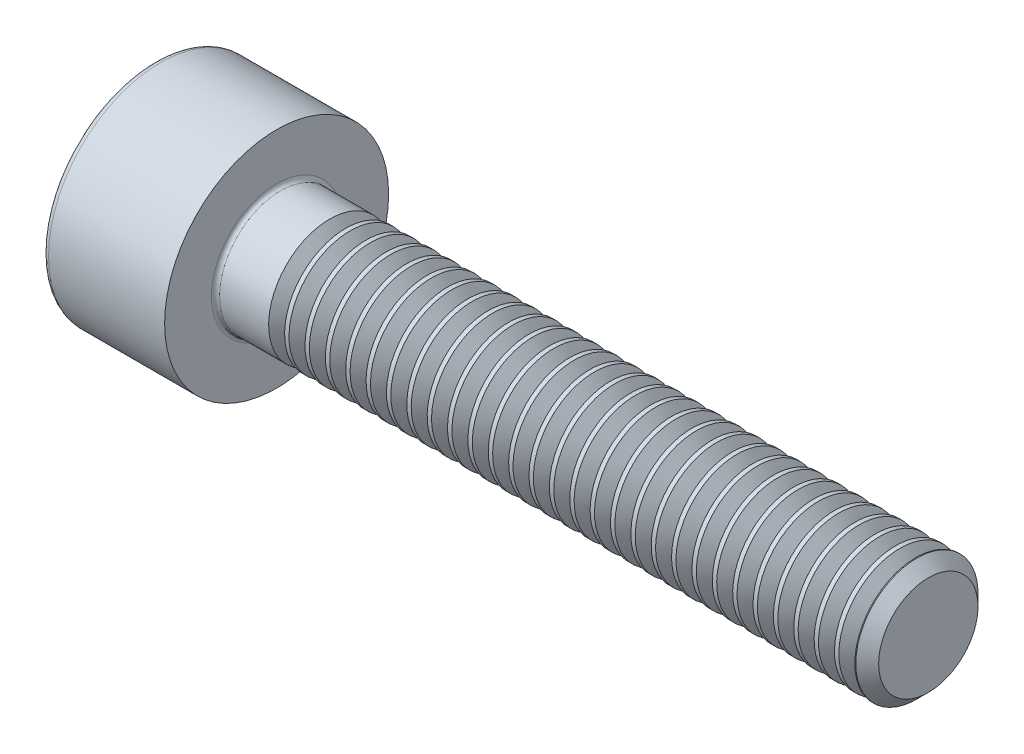
SolidWorks part; units mm, degrees
revolve "Base-Revolve" add sketch "BodySke"
sketch "BodySke" plane through (0, 0, 0) normal (0, 0, 1) x (1, 0, 0)
  line L0 (0, 0) -> (0, 2.75)
  line L1 (0, 2.75) -> (3, 2.75)
  line L2 (3, 2.75) -> (3, 1.5)
  line L3 (3, 1.5) -> (18.7195, 1.5)
  line L4 (19, 1.2195) -> (19, 0)
  line L5 (19, 0) -> (0, 0)
  line L6 (-31.75, 0) -> (127, 0) construction
  line L8 (19, 1.2195) -> (18.7195, 1.5)
  line L10 (19, -1.2195) -> (18.7195, -1.5) construction
  line L11 (3.5, 9.525) -> (3.5, 3.175) construction
  line L12 (3, 9.525) -> (3, 3.175) construction
  line L13 (-41, 9.525) -> (-41, 3.175) construction
  dimension "Head_ht" = 3
  dimension "Length" = 16
  dimension "Body_ch_ang" = 45
  dimension "Diameter" = 3
  dimension "Minor_dia" = 2.439
  dimension "Advance" = 0.5
  dimension "Thread_nom" = 16
  dimension "Thread_length" = 60
  dimension "Head_dia" = 5.5
cosmetic thread "ThreadCosmetic" [suppressed]
fillet "Fillet1" radius 0.1 1 edges at (3, 0, 1.5)
fillet "Fillet2" radius 0.15 1 edges at (0, 0, 2.75)
material "201 Annealed Stainless Steel (SS)"
ref_plane "Plane1" through (0, 0, 0) normal (0, 0, 1) x (1, 0, 0)
ref_plane "Plane2" through (0, 0, 0) normal (0, 1, 0) x (1, 0, 0)
ref_plane "Plane3" through (0, 0, 0) normal (1, 0, 0) x (0, 0, -1)
sketch "Sketch2" plane through (0, 0, 0) normal (0, 0, 1) x (1, 0, 0)
  line L0 (0, 1.28) -> (1.3, 1.28)
  line L1 (1.3, 1.28) -> (2.039, 0)
  line L2 (-31.75, 0) -> (127, 0) construction
  line L3 (2.039, 0) -> (0, 0)
  line L4 (0, 0) -> (0, 1.28)
  line L6 (0, 0) -> (47.625, 0) construction
  dimension "D1" = 1.28
  dimension "D2" = 60
  dimension "Depth" = 1.3
revolve "Hex-PreBroach" cut sketch "Sketch2" angle 360 about L6
sketch "Sketch3" plane through (0, 0, 0) normal (-1, 0, 0) x (0, 0.5, 0.866)
  line L0 (0.739, 1.28) -> (-0.739, 1.28)
  line L1 (-0.739, 1.28) -> (-1.478, 0)
  line L2 (0.739, 1.28) -> (1.478, 0)
  line L3 (0.739, -1.28) -> (1.478, 0)
  line L4 (0.739, -1.28) -> (-0.739, -1.28)
  line L5 (-0.739, -1.28) -> (-1.478, 0)
  dimension "D1" = 1.28
  dimension "D2" = 1.28
  dimension "Hex_size" = 2.56
extrude "Hex" cut sketch "Sketch3" against normal blind 1.3
sketch "ThdSchSke" plane through (0, 0, 0) normal (0, 0, 1) x (1, 0, 0)
  line L0 (4.5, -1.2195) -> (4.3036, -1.5)
  line L1 (4.5, -1.2195) -> (4.6964, -1.5)
  line L2 (4.6964, -1.5) -> (4.6964, -1.875)
  line L3 (-3.175, 0) -> (5.1513, 0) construction
  line L4 (0, 2.6) -> (0, -2.6) construction
  line L5 (4.6964, -1.875) -> (4.3036, -1.875)
  line L6 (4.3036, -1.875) -> (4.3036, -1.5)
  dimension "Thread_minor" = 2.439
  dimension "Diameter" = 3
  dimension "Start" = 4.5
revolve "ThreadSchematic" cut sketch "ThdSchSke" angle 360 about L3
pattern_linear "ThdSchPat" count 29 spacing 0.5 along (1, 0, 0) of "ThreadSchematic"
equation "\"D2@Sketch3\" = \"Hex_size@Sketch3\" / 2"
equation "\"D1@Sketch3\" = \"Hex_size@Sketch3\" / 2"
equation "\"D1@Sketch2\" = \"Hex_size@Sketch3\" / 2"
equation "\"Thread_minor@ThreadCosmetic\"  =  \"Minor_dia@BodySke\""
equation "\"Depth@Sketch2\" =  \"Key_eng@Hex\""
equation "\"Thread_length@ThreadCosmetic\" = ((sgn( (\"Length@BodySke\" - \"Advance@BodySke\" * 3.0) - \"Thread_nom@BodySke\" )-1)*( (\"Length@BodySke\" - \"Advance@BodySke\" * 3.0) - \"Thread_nom@BodySke\" ))/-2+ \"Thread_nom@BodySke\""
equation "\"Thread_minor@ThdSchSke\" = \"Minor_dia@BodySke\""
equation "\"Diameter@ThdSchSke\" = \"Diameter@BodySke\""
equation "\"Overcut@ThdSchSke\" = \"Diameter@BodySke\" * 1.25"
equation "\"Start@ThdSchSke\" = \"Head_ht@BodySke\" + \"Length@BodySke\" - \"Thread_length@ThreadCosmetic\"  '---Non-countersunk---"
equation "\"Num_threads@ThdSchPat\" = int( \"Thread_length@ThreadCosmetic\" / \"Advance@BodySke\" + 0.999 )  + 1"
equation "\"Advance@ThdSchPat\" = \"Thread_length@ThreadCosmetic\" /  (\"Num_threads@ThdSchPat\" - 1) 'relax it"
equation "\"Num_threads@ThdSchPat\" = \"Num_threads@ThdSchPat\" - sgn( \"Num_threads@ThdSchPat\" - 1) '---chamfered tips only---"
